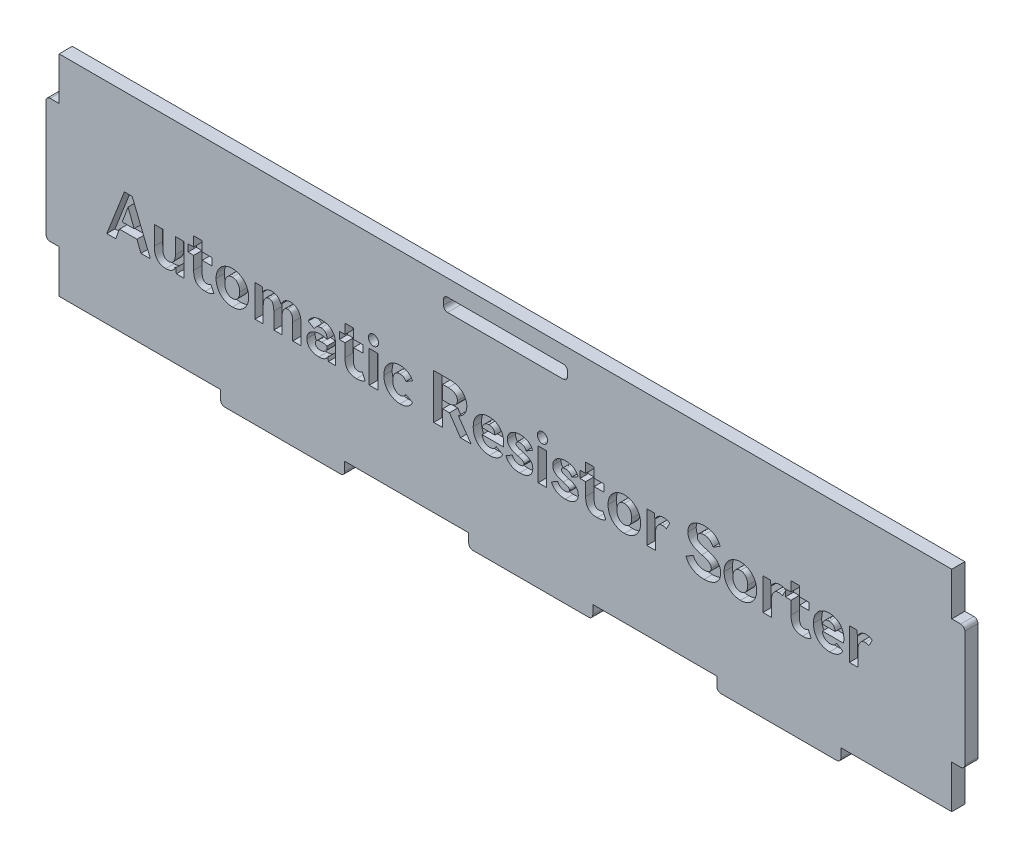
SolidWorks part; units mm, degrees
ref_plane "Front Plane" through (0, 0, 0) normal (0, 0, 1) x (1, 0, 0)
ref_plane "Top Plane" through (0, 0, 0) normal (0, 1, 0) x (1, 0, 0)
ref_plane "Right Plane" through (0, 0, 0) normal (1, 0, 0) x (0, 0, -1)
sketch "Sketch1" plane through (0, 0, 0) normal (0, 0, 1) x (1, 0, 0)
  line L1 (-107.9525, -25.4) -> (107.9525, -25.4)
  line L2 (-107.9525, -25.4) -> (-107.9525, 25.4)
  line L3 (-107.9525, 25.4) -> (107.9525, 25.4)
  line L4 (107.9525, -25.4) -> (107.9525, 25.4)
  line L5 (-107.9525, -25.4) -> (107.9525, 25.4) construction
  line L6 (-107.9525, 25.4) -> (107.9525, -25.4) construction
  point P0 (0, 0)
  dimension "D1" = 50.8
  dimension "D2" = 215.905
extrude "Boss-Extrude1" add sketch "Sketch1" along normal blind 3.175
sketch "Sketch2" plane through (107.9525, 0, 0) normal (1, 0, 0) x (0, 0, -1)
  line L0 (0, 0) -> (-3.175, 0) construction
  line L1 (-3.175, -25.4) -> (-3.175, 25.4) construction
  line L2 (0, -25.4) -> (0, 25.4) construction
  line L3 (-3.175, 15) -> (0, 15)
  line L4 (-3.175, 15) -> (-3.175, -15)
  line L5 (-3.175, -15) -> (0, -15)
  line L6 (0, 15) -> (0, -15)
  line L7 (-3.175, 15) -> (0, -15) construction
  line L8 (-3.175, -15) -> (0, 15) construction
  point P5 (-1.5875, 0)
  dimension "D1" = 30
extrude "Boss-Extrude2" add sketch "Sketch2" along normal blind 3.175
sketch "Sketch3" plane through (-107.9525, 0, 0) normal (-1, 0, 0) x (0, 0, 1)
  line L0 (0, 0) -> (3.175, 0) construction
  line L1 (3.175, 25.4) -> (3.175, -25.4) construction
  line L3 (0, -15) -> (3.175, -15)
  line L4 (0, -15) -> (0, 15)
  line L5 (0, 15) -> (3.175, 15)
  line L6 (3.175, -15) -> (3.175, 15)
  line L7 (0, -15) -> (3.175, 15) construction
  line L8 (0, 15) -> (3.175, -15) construction
  point P5 (1.5875, 0)
  dimension "D1" = 30
extrude "Boss-Extrude3" add sketch "Sketch3" along normal blind 3.175
sketch "Sketch4" plane through (0, -25.4, 0) normal (0, -1, 0) x (1, 0, 0)
  line L0 (107.9525, 1.5875) -> (81.1225, 1.5875) construction
  line L1 (107.9525, 3.175) -> (107.9525, 0) construction
  line L2 (-107.9525, 3.175) -> (107.9525, 3.175) construction
  line L3 (81.1225, 3.175) -> (51.1225, 3.175)
  line L4 (81.1225, 3.175) -> (81.1225, 0)
  line L5 (81.1225, 0) -> (51.1225, 0)
  line L6 (51.1225, 3.175) -> (51.1225, 0)
  line L7 (-107.9525, 0) -> (107.9525, 0) construction
  line L8 (21.1225, 3.175) -> (21.1225, 0)
  line L9 (21.1225, 3.175) -> (-8.8775, 3.175)
  line L10 (-8.8775, 3.175) -> (-8.8775, 0)
  line L11 (21.1225, 0) -> (-8.8775, 0)
  line L12 (-38.8775, 3.175) -> (-38.8775, 0)
  line L13 (-38.8775, 3.175) -> (-68.8775, 3.175)
  line L14 (-68.8775, 3.175) -> (-68.8775, 0)
  line L15 (-38.8775, 0) -> (-68.8775, 0)
  line L16 (81.1225, 3.175) -> (21.1225, 3.175) construction
  dimension "D1" = 26.83
  dimension "D2" = 30
  dimension "D4" = 60
  dimension "D3" = 3
extrude "Boss-Extrude4" add sketch "Sketch4" along normal blind 3.175
sketch "Sketch5" plane through (0, 0, 3.175) normal (0, 0, 1) x (1, 0, 0)
  line L0 (0, 25.4) -> (0, 19.8125) construction
  line L1 (107.9525, 25.4) -> (-107.9525, 25.4) construction
  line L3 (-15, 18.225) -> (15, 18.225)
  line L4 (-15, 18.225) -> (-15, 21.4)
  line L5 (-15, 21.4) -> (15, 21.4)
  line L6 (15, 18.225) -> (15, 21.4)
  line L7 (-15, 18.225) -> (15, 21.4) construction
  line L8 (-15, 21.4) -> (15, 18.225) construction
  dimension "D1" = 30
  dimension "D2" = 3.175
  dimension "D3" = 4
extrude "Cut-Extrude1" cut sketch "Sketch5" against normal blind 10
fillet "Fillet1" radius 1 10 edges at (111.1275, -15, 1.5875) (111.1275, 15, 1.5875) (-111.1275, 15, 1.5875) (-111.1275, -15, 1.5875) (-68.8775, -28.575, 1.5875) (-38.8775, -28.575, 1.5875) (-8.8775, -28.575, 1.5875) (21.1225, -28.575, 1.5875) (81.1225, -28.575, 1.5875) (51.1225, -28.575, 1.5875)
fillet "Fillet2" radius 1 4 edges at (15, 18.225, 1.5875) (15, 21.4, 1.5875) (-15, 21.4, 1.5875) (-15, 18.225, 1.5875)
sketch "Sketch6" plane through (0, 0, 3.175) normal (0, 0, 1) x (1, 0, 0)
  text T0 "Automatic Resistor Sorter" font "HarmonyOS Sans SC" height in points 40
extrude "Cut-Extrude2" cut sketch "Sketch6" against normal blind 2
